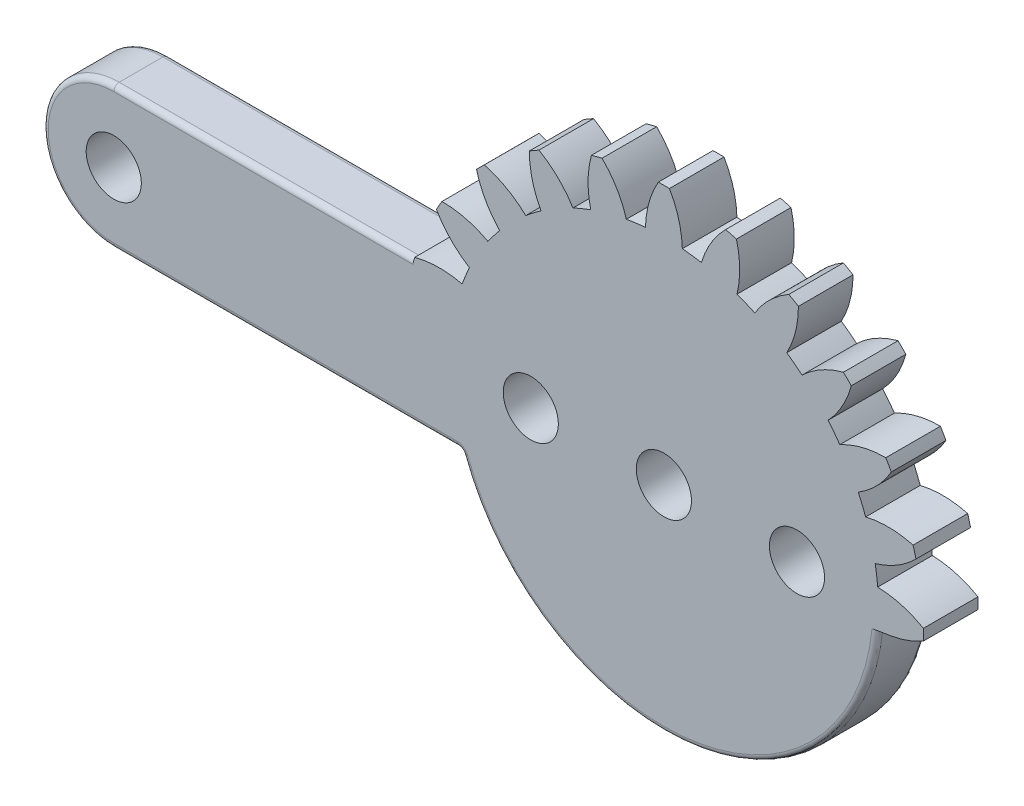
SolidWorks part; units mm, degrees
ref_plane "前视基准面" through (0, 0, 0) normal (0, 0, 1) x (1, 0, 0)
ref_plane "上视基准面" through (0, 0, 0) normal (0, 1, 0) x (1, 0, 0)
ref_plane "右视基准面" through (0, 0, 0) normal (1, 0, 0) x (0, 0, -1)
sketch "草图1" plane through (0, 0, 0) normal (0, 0, 1) x (1, 0, 0)
  line L6 (39.1409, -3.5483) -> (41.5706, -3.148)
  line L7 (-45.7189, 13) -> (-100.75, 13)
  line L8 (-100.75, -13) -> (-37.0891, -13)
  circle A4 centre (24.375, 0) radius 5.05
  circle A5 centre (0, 0) radius 5.05
  circle A6 centre (-24.375, 0) radius 5.05
  circle A7 centre (-100.75, 0) radius 5.05
  arc A96 (-37.0891, -13) -> (39.1409, -3.5483) centre (0, 0) ccw
  arc A97 (41.5706, -3.148) -> (47.5204, -1.0143) centre (38.718, 14.1686) ccw
  arc A98 (47.5204, -1.0143) -> (47.5204, 1.0143) centre (0, 0) ccw
  arc A99 (47.5204, 1.0143) -> (39.1562, 3.3759) centre (38.718, -14.1686) ccw
  arc A100 (39.1562, 3.3759) -> (38.6957, 6.8735) centre (0, 0) ccw
  arc A101 (38.6957, 6.8735) -> (46.1637, 11.3195) centre (33.7316, 23.7068) ccw
  arc A102 (46.1637, 11.3195) -> (45.6387, 13.2789) centre (0, 0) ccw
  arc A103 (45.6387, 13.2789) -> (36.9482, 13.3953) centre (41.0658, -3.6649) ccw
  arc A104 (36.9482, 13.3953) -> (35.5982, 16.6544) centre (0, 0) ccw
  arc A105 (35.5982, 16.6544) -> (41.661, 22.8818) centre (26.4465, 31.6294) ccw
  arc A106 (41.661, 22.8818) -> (40.6468, 24.6386) centre (0, 0) ccw
  arc A107 (40.6468, 24.6386) -> (32.2223, 22.5017) centre (40.6151, 7.0886) ccw
  arc A108 (32.2223, 22.5017) -> (30.0747, 25.3004) centre (0, 0) ccw
  arc A109 (30.0747, 25.3004) -> (34.3192, 32.8848) centre (17.359, 37.3965) ccw
  arc A110 (34.3192, 32.8848) -> (32.8848, 34.3192) centre (0, 0) ccw
  arc A111 (32.8848, 34.3192) -> (25.3004, 30.0747) centre (37.3965, 17.359) ccw
  arc A112 (25.3004, 30.0747) -> (22.5017, 32.2223) centre (0, 0) ccw
  arc A113 (22.5017, 32.2223) -> (24.6386, 40.6468) centre (7.0886, 40.6151) ccw
  arc A114 (24.6386, 40.6468) -> (22.8818, 41.661) centre (0, 0) ccw
  arc A115 (22.8818, 41.661) -> (16.6544, 35.5982) centre (31.6294, 26.4465) ccw
  arc A116 (16.6544, 35.5982) -> (13.3953, 36.9482) centre (0, 0) ccw
  arc A117 (13.3953, 36.9482) -> (13.2789, 45.6387) centre (-3.6649, 41.0658) ccw
  arc A118 (13.2789, 45.6387) -> (11.3195, 46.1637) centre (0, 0) ccw
  arc A119 (11.3195, 46.1637) -> (6.8735, 38.6957) centre (23.7068, 33.7316) ccw
  arc A120 (6.8735, 38.6957) -> (3.3759, 39.1562) centre (0, 0) ccw
  arc A121 (3.3759, 39.1562) -> (1.0143, 47.5204) centre (-14.1686, 38.718) ccw
  arc A122 (1.0143, 47.5204) -> (-1.0143, 47.5204) centre (0, 0) ccw
  arc A123 (-1.0143, 47.5204) -> (-3.3759, 39.1562) centre (14.1686, 38.718) ccw
  arc A124 (-3.3759, 39.1562) -> (-6.8735, 38.6957) centre (0, 0) ccw
  arc A125 (-6.8735, 38.6957) -> (-11.3195, 46.1637) centre (-23.7068, 33.7316) ccw
  arc A126 (-11.3195, 46.1637) -> (-13.2789, 45.6387) centre (0, 0) ccw
  arc A127 (-13.2789, 45.6387) -> (-13.3953, 36.9482) centre (3.6649, 41.0658) ccw
  arc A128 (-13.3953, 36.9482) -> (-16.6544, 35.5982) centre (0, 0) ccw
  arc A129 (-16.6544, 35.5982) -> (-22.8818, 41.661) centre (-31.6294, 26.4465) ccw
  arc A130 (-22.8818, 41.661) -> (-24.6386, 40.6468) centre (0, 0) ccw
  arc A131 (-24.6386, 40.6468) -> (-22.5017, 32.2223) centre (-7.0886, 40.6151) ccw
  arc A132 (-22.5017, 32.2223) -> (-25.3004, 30.0747) centre (0, 0) ccw
  arc A133 (-25.3004, 30.0747) -> (-32.8848, 34.3192) centre (-37.3965, 17.359) ccw
  arc A134 (-32.8848, 34.3192) -> (-34.3192, 32.8848) centre (0, 0) ccw
  arc A135 (-34.3192, 32.8848) -> (-30.0747, 25.3004) centre (-17.359, 37.3965) ccw
  arc A136 (-30.0747, 25.3004) -> (-32.2223, 22.5017) centre (0, 0) ccw
  arc A137 (-32.2223, 22.5017) -> (-40.6468, 24.6386) centre (-40.6151, 7.0886) ccw
  arc A138 (-40.6468, 24.6386) -> (-41.661, 22.8818) centre (0, 0) ccw
  arc A139 (-41.661, 22.8818) -> (-35.5982, 16.6544) centre (-26.4465, 31.6294) ccw
  arc A140 (-35.5982, 16.6544) -> (-36.9482, 13.3953) centre (0, 0) ccw
  arc A141 (-36.9482, 13.3953) -> (-45.6387, 13.2789) centre (-41.0658, -3.6649) ccw
  arc A142 (-45.6387, 13.2789) -> (-45.7189, 13) centre (0, 0) ccw
  arc A143 (-100.75, 13) -> (-100.75, -13) centre (-100.75, 0) ccw
  dimension "D1" = 39.3014
  dimension "D3" = 13
  dimension "D4" = 10.1
  dimension "D5" = 47.5313
  dimension "D6" = 48.75
  dimension "D7" = 24.375
  dimension "D2" = 100.75
extrude "凸台-拉伸1" add sketch "草图1" along normal blind 10
fillet "圆角1" radius 1 9 edges at (-73.2345, 13, 0) (-113.75, 0, 0) (-68.9196, -13, 0) (-73.2345, 13, 10) (-68.9196, -13, 10) (4.8359, -39.0028, 0) (-37.0891, -13, 5) (4.8359, -39.0028, 10) (-113.75, 0, 10)
